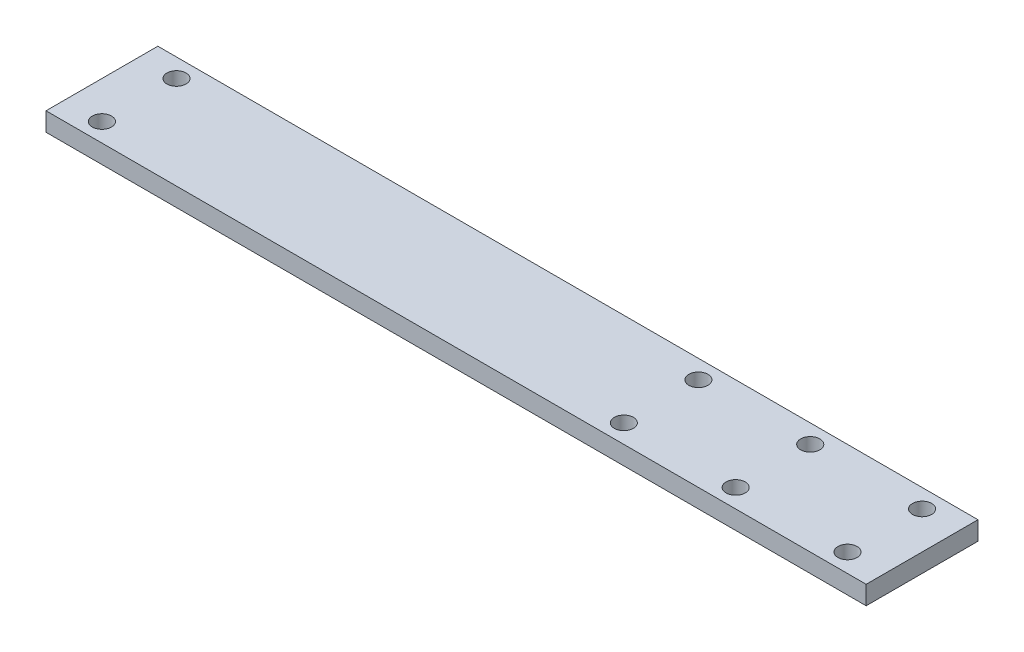
SolidWorks part; units mm, degrees
ref_plane "Front Plane" through (0, 0, 0) normal (0, 0, 1) x (1, 0, 0)
ref_plane "Top Plane" through (0, 0, 0) normal (0, 1, 0) x (1, 0, 0)
ref_plane "Right Plane" through (0, 0, 0) normal (1, 0, 0) x (0, 0, -1)
sketch "Sketch1" plane through (0, 0, 0) normal (0, 1, 0) x (1, 0, 0)
  line L1 (-139.7, 19.05) -> (139.7, 19.05)
  line L2 (-139.7, 19.05) -> (-139.7, -19.05)
  line L3 (-139.7, -19.05) -> (139.7, -19.05)
  line L4 (139.7, 19.05) -> (139.7, -19.05)
  line L5 (-139.7, 19.05) -> (139.7, -19.05) construction
  line L6 (-139.7, -19.05) -> (139.7, 19.05) construction
  point P0 (0, 0)
  dimension "D1" = 279.4
  dimension "D2" = 38.1
extrude "Boss-Extrude1" add sketch "Sketch1" along normal blind 6.35
hole_wizard "1/4 Clearance Hole1" positions "Sketch3" profile "Sketch2" hole size "1/4" standard "Ansi Inch" end condition up to next
sketch "Sketch3" plane through (0, 6.35, 0) normal (0, 1, 0) x (-1, 0, 0)
  line L0 (127, -12.7) -> (127, 12.7) construction
  line L3 (127, -12.7) -> (-127, -12.7) construction
  line L5 (127, 12.7) -> (-127, 12.7) construction
  line L7 (-139.7, 19.05) -> (-139.7, -19.05) construction
  point P0 (127, 12.7)
  point P1 (127, -12.7)
  point P10 (127, 0)
  point P29 (-127, -12.7)
  point P31 (-127, 12.7)
  point P41 (-88.9, -12.7)
  point P43 (-88.9, 12.7)
  point P45 (-50.8, -12.7)
  point P47 (-50.8, 12.7)
  dimension "D1" = 25.4
  dimension "D2" = 12.7
  dimension "D3" = 38.1
  dimension "D4" = 38.1
  dimension "D5" = 177.8
sketch "Sketch2" plane through (-127, 6.35, 12.7) normal (1, 0, 0) x (0, 0, 1)
  line L0 (0, 0) -> (0, 6.35)
  line L1 (0, 6.35) -> (3.2639, 6.35)
  line L2 (3.2639, 6.35) -> (3.2639, 0)
  line L5 (3.2639, 0) -> (0, 0)
  line L11 (0, -6.35) -> (0, 107.95) construction
  dimension "Thru Hole Dia." = 6.5278
  dimension "Thru Hole Depth" = 6.35
